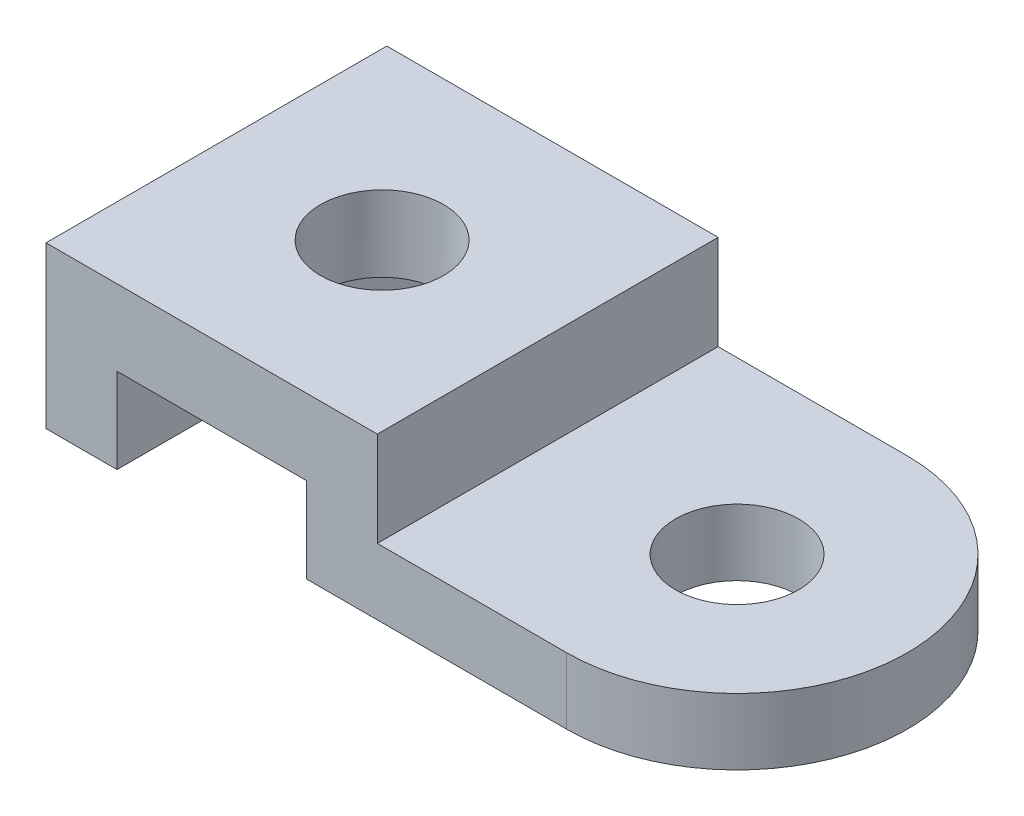
SolidWorks part; units mm, degrees
ref_plane "Ön Düzlem" through (0, 0, 0) normal (0, 0, 1) x (1, 0, 0)
ref_plane "Üst Düzlem" through (0, 0, 0) normal (0, 1, 0) x (1, 0, 0)
ref_plane "Sağ Düzlem" through (0, 0, 0) normal (1, 0, 0) x (0, 0, -1)
sketch "Çizim2" plane through (0, 0, 0) normal (0, 1, 0) x (1, 0, 0)
  line L0 (35, -36) -> (75, -36)
  line L1 (-35, -36) -> (-35, 36)
  line L2 (-35, -36) -> (35, -36)
  line L3 (-35, 36) -> (35, 36)
  line L4 (35, -36) -> (35, 36)
  line L5 (75, 36) -> (75, -36) construction
  line L6 (75, 36) -> (35, 36)
  circle A0 centre (0, 0) radius 13
  circle A1 centre (75, 0) radius 13
  arc A2 (75, -36) -> (75, 36) centre (75, 0) ccw
  dimension "D1" = 26
  dimension "D7" = 26
  dimension "D8" = 36
  dimension "D2" = 36
  dimension "D3" = 70
  dimension "D4" = 72
  dimension "D5" = 35
  dimension "D6" = 40
ref_plane "Düzlem1" through (0, 0, 36) normal (0, 0, 1) x (1, 0, 0)
sketch "Çizim3" plane through (0, 0, 36) normal (0, 0, 1) x (1, 0, 0)
  line L0 (-35, 0) -> (-35, -34)
  line L2 (-35, -34) -> (-20, -34)
  line L3 (-20, -34) -> (-20, -16)
  line L4 (-20, -16) -> (20, -16)
  line L5 (20, -16) -> (20, -34)
  line L6 (-35, 0) -> (35, 0)
  line L7 (-35, 0) -> (35, 0) construction
  line L9 (35, 0) -> (75, 0) construction
  line L11 (35, 0) -> (35, -20)
  line L12 (20, -34) -> (75, -34)
  line L15 (75, -20) -> (35, -20)
  line L16 (75, -20) -> (111, -20)
  line L17 (75, -34) -> (111, -34)
  line L18 (111, -34) -> (111, -20)
  dimension "D1" = 34
  dimension "D2" = 15
  dimension "D3" = 18
  dimension "D4" = 55
  dimension "D5" = 18
  dimension "D6" = 20
  dimension "D7" = 55
  dimension "D8" = 14
  dimension "D9" = 15
  dimension "D10" = 36
  dimension "D11" = 40
extrude "Yükseklik-Ekstrüzyon1" add sketch "Çizim2" against normal blind 34 contours L2 L4 L3 L1 A0 | L5 L6 L4 L0 A1 | A2 L5 A1
extrude "Kes-Ekstrüzyon4" cut sketch "Çizim3" against normal through all flip side to cut contours L5 L12 L17 L18 L16 L15 L11 L6 L0 L2 L3 L4
